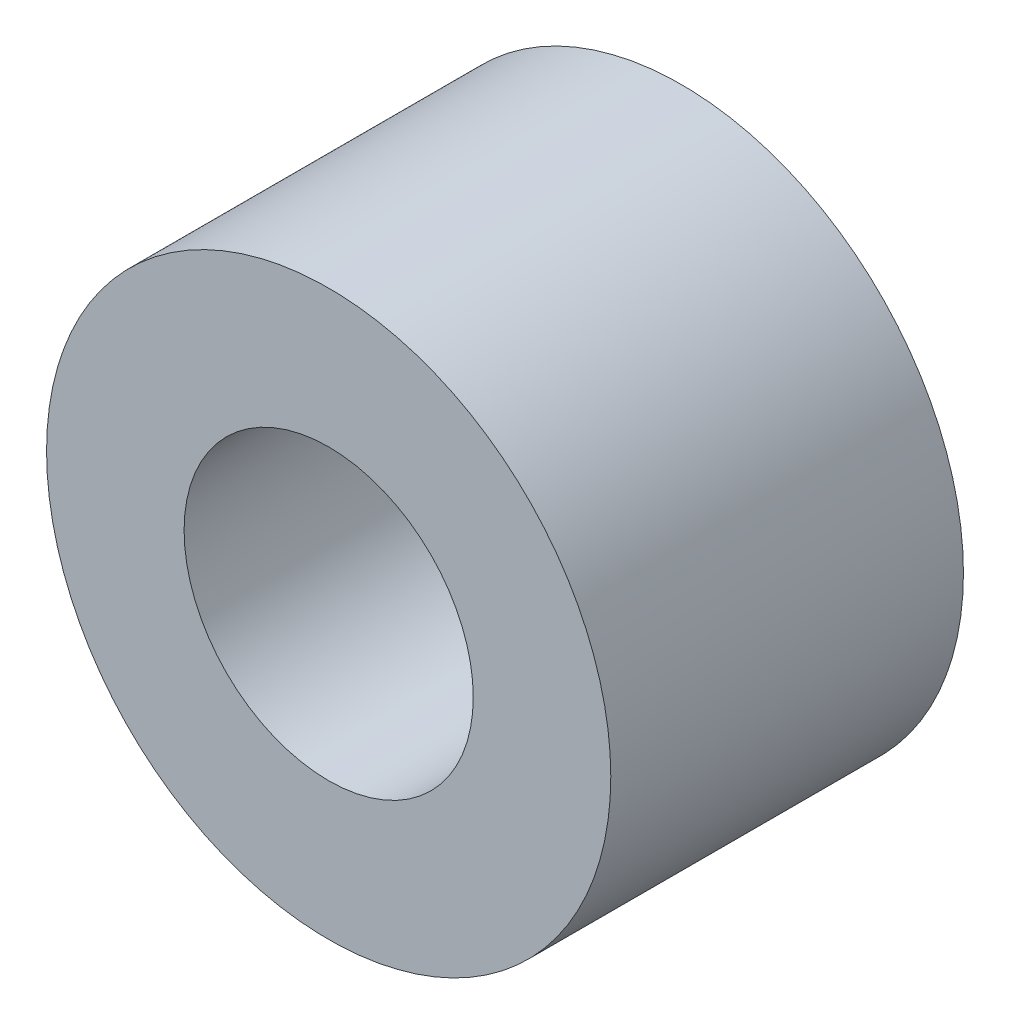
SolidWorks part; units mm, degrees
ref_plane "Front Plane" through (0, 0, 0) normal (0, 0, 1) x (1, 0, 0)
ref_plane "Top Plane" through (0, 0, 0) normal (0, 1, 0) x (1, 0, 0)
ref_plane "Right Plane" through (0, 0, 0) normal (1, 0, 0) x (0, 0, -1)
sketch "Sketch1" plane through (0, 0, 0) normal (0, 0, 1) x (1, 0, 0)
  circle A0 centre (0, 0) radius 4.1
  circle A1 centre (0, 0) radius 8
  dimension "D1" = 8.2
  dimension "D2" = 16
extrude "Boss-Extrude1" add sketch "Sketch1" along normal blind 10
